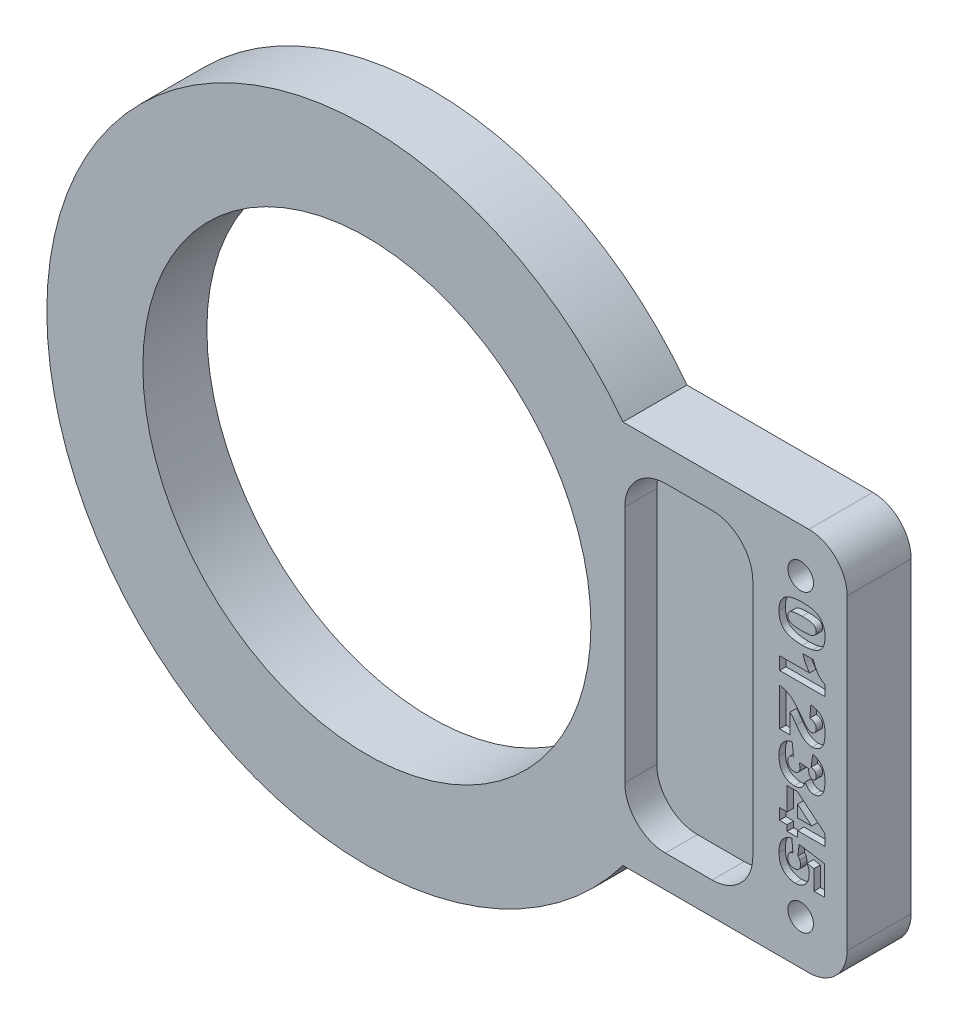
SolidWorks part; units mm, degrees
ref_plane "Front Plane" through (0, 0, 0) normal (0, 0, 1) x (1, 0, 0)
ref_plane "Top Plane" through (0, 0, 0) normal (0, 1, 0) x (1, 0, 0)
ref_plane "Right Plane" through (0, 0, 0) normal (1, 0, 0) x (0, 0, -1)
sketch "Model" plane through (0, 0, 0) normal (0, 0, 1) x (1, 0, 0)
  line L0 (100.7964, -32.5754) -> (97.3961, -32.5754)
  line L1 (97.3961, -32.5754) -> (97.3961, -31.6358)
  line L2 (97.3961, -31.6358) -> (99.6242, -31.6358)
  line L3 (99.1385, -30.6596) -> (99.9, -30.6596)
  line L4 (100.7964, -31.8068) -> (100.7964, -32.5754)
  line L5 (97.3961, -36.3039) -> (97.3961, -33.5172)
  line L6 (99.6538, -34.5161) -> (99.7287, -33.5857)
  line L7 (98.1534, -34.8535) -> (98.1534, -36.3039)
  line L8 (98.1534, -36.3039) -> (97.3961, -36.3039)
  line L9 (99.772, -37.6015) -> (99.9295, -36.7234)
  line L10 (98.2788, -36.6732) -> (98.4016, -37.6015)
  line L11 (98.8394, -37.7541) -> (99.5029, -37.802)
  line L12 (98.7415, -41.4121) -> (99.7934, -41.4121)
  line L13 (99.7934, -41.4121) -> (98.7415, -40.518)
  line L14 (98.7415, -40.518) -> (98.7415, -41.4121)
  line L15 (98.0209, -41.4121) -> (98.0209, -39.7201)
  line L16 (98.0209, -39.7201) -> (98.7848, -39.7201)
  line L17 (98.7848, -39.7201) -> (100.7964, -41.4121)
  line L18 (100.7964, -41.4121) -> (100.7964, -42.2217)
  line L19 (100.7964, -42.2217) -> (98.7415, -42.2217)
  line L20 (98.7415, -42.2217) -> (98.7415, -42.6414)
  line L21 (98.7415, -42.6414) -> (98.0209, -42.6414)
  line L22 (98.0209, -42.6414) -> (98.0209, -42.2217)
  line L23 (98.0209, -42.2217) -> (97.3961, -42.2217)
  line L24 (97.3961, -42.2217) -> (97.3961, -41.4121)
  line L25 (97.3961, -41.4121) -> (98.0209, -41.4121)
  line L26 (100.7393, -43.307) -> (100.7393, -45.5122)
  line L27 (100.7393, -45.5122) -> (99.9978, -45.5122)
  line L28 (99.9978, -45.5122) -> (99.9978, -44.0185)
  line L29 (99.9978, -44.0185) -> (99.4963, -43.9387)
  line L30 (98.2625, -42.8921) -> (98.3654, -43.8317)
  line L31 (98.8282, -43.8042) -> (98.9423, -43.0129)
  line L32 (98.9423, -43.0129) -> (100.7393, -43.307)
  line L33 (99.6589, -21.5138) -> (85.3342, -21.5138)
  line L34 (85.3342, -51.5138) -> (99.6589, -51.5138)
  line L35 (102.8339, -48.3388) -> (102.8339, -24.6888)
  line L36 (92.3025, -49.0138) -> (88.6525, -49.0138)
  line L37 (85.4775, -45.8388) -> (85.4775, -27.1888)
  line L38 (88.6525, -24.0138) -> (92.3025, -24.0138)
  line L39 (95.4775, -27.1888) -> (95.4775, -45.8388)
  circle A0 centre (99.2184, -24.9849) radius 1
  circle A1 centre (99.2184, -48.0427) radius 1
  circle A2 centre (65.3339, -36.5138) radius 17.5
  spline S0 degree 3 poles (99.9443, -28.3794) (99.7883, -28.3109) (99.4999, -28.2767) (99.0789, -28.2767) knots 8 8 8 8 9 9 9 9
  spline S1 degree 3 poles (99.9489, -29.0509) (100.1018, -28.9757) (100.1782, -28.8628) (100.1782, -28.7122) (100.1782, -28.5588) (100.1002, -28.4477) (99.9443, -28.3794) knots 6 6 6 6 7 7 7 8 8 8 8
  spline S2 degree 3 poles (98.0724, -28.962) (98.1381, -29.0313) (98.2431, -29.0822) (98.5285, -29.1475) (98.7512, -29.1638) (99.0539, -29.1638) (99.4978, -29.1638) (99.796, -29.1263) (99.9489, -29.0509) knots 3 3 3 3 4 4 5 5 5 6 6 6 6
  spline S3 degree 3 poles (98.2069, -28.3896) (98.051, -28.4648) (97.973, -28.5739) (97.973, -28.7168) (97.973, -28.8111) (98.0061, -28.8929) (98.0724, -28.962) knots 1 1 1 1 2 2 2 3 3 3 3
  spline S4 degree 3 poles (99.0789, -28.2767) (98.6534, -28.2767) (98.3623, -28.3144) (98.2069, -28.3896) knots 0 0 0 0 1 1 1 1
  spline S5 degree 3 poles (97.868, -27.6109) (97.9913, -27.5304) (98.1595, -27.4677) (98.5866, -27.378) (98.8231, -27.3555) (99.0815, -27.3555) knots 11 11 11 11 12 12 13 13 13 13
  spline S6 degree 3 poles (97.4735, -28.0375) (97.5632, -27.8639) (97.6947, -27.7217) (97.868, -27.6109) knots 10 10 10 10 11 11 11 11
  spline S7 degree 3 poles (97.761, -29.7797) (97.4796, -29.5743) (97.339, -29.2209) (97.339, -28.7191) (97.339, -28.4378) (97.3838, -28.2107) (97.4735, -28.0375) knots 8 8 8 8 9 9 9 10 10 10 10
  spline S8 degree 3 poles (99.8724, -29.994) (99.6232, -30.0562) (99.3633, -30.0875) (99.0927, -30.0875) (98.4862, -30.0875) (98.0423, -29.9848) (97.761, -29.7797) knots 6 6 6 6 7 7 7 8 8 8 8
  spline S9 degree 3 poles (100.2159, -29.8673) (100.1176, -29.9198) (100.0034, -29.9621) (99.8724, -29.994) knots 5 5 5 5 6 6 6 6
  spline S10 degree 3 poles (100.4962, -29.6518) (100.4076, -29.743) (100.3138, -29.8148) (100.2159, -29.8673) knots 4 4 4 4 5 5 5 5
  spline S11 degree 3 poles (100.4152, -27.6988) (100.669, -27.9274) (100.7964, -28.276) (100.7964, -28.7443) (100.7964, -28.9693) (100.7684, -29.1538) (100.6573, -29.4428) (100.5854, -29.5605) (100.4962, -29.6518) knots 1 1 1 1 2 2 2 3 3 4 4 4 4
  spline S12 degree 3 poles (99.0815, -27.3555) (99.717, -27.3555) (100.1614, -27.47) (100.4152, -27.6988) knots 0 0 0 0 1 1 1 1
  spline S13 degree 3 poles (99.6242, -31.6358) (99.5085, -31.4837) (99.4148, -31.3367) (99.3434, -31.1945) knots 3 3 3 3 4 4 4 4
  spline S14 degree 3 poles (99.3434, -31.1945) (99.2721, -31.0523) (99.2038, -30.8742) (99.1385, -30.6596) knots 4 4 4 4 5 5 5 5
  spline S15 degree 3 poles (99.9, -30.6596) (100.0019, -30.9758) (100.1242, -31.2215) (100.2669, -31.3963) knots 6 6 6 6 7 7 7 7
  spline S16 degree 3 poles (100.2669, -31.3963) (100.4101, -31.5711) (100.5865, -31.7079) (100.7964, -31.8068) knots 7 7 7 7 8 8 8 8
  spline S17 degree 3 poles (97.3961, -33.5172) (97.6713, -33.5493) (97.9302, -33.6461) (98.1728, -33.8079) knots 1 1 1 1 2 2 2 2
  spline S18 degree 3 poles (98.1728, -33.8079) (98.4148, -33.97) (98.7013, -34.2735) (99.031, -34.7189) knots 2 2 2 2 3 3 3 3
  spline S19 degree 3 poles (99.031, -34.7189) (99.2333, -34.9911) (99.3867, -35.1651) (99.4917, -35.2413) knots 3 3 3 3 4 4 4 4
  spline S20 degree 3 poles (99.4917, -35.2413) (99.5967, -35.3173) (99.6961, -35.3552) (99.7904, -35.3552) knots 4 4 4 4 5 5 5 5
  spline S21 degree 3 poles (99.7904, -35.3552) (99.8923, -35.3552) (99.9795, -35.3178) (100.0518, -35.2423) knots 5 5 5 5 6 6 6 6
  spline S22 degree 3 poles (100.0518, -35.2423) (100.1237, -35.1672) (100.1599, -35.0726) (100.1599, -34.9585) knots 6 6 6 6 7 7 7 7
  spline S23 degree 3 poles (100.1599, -34.9585) (100.1599, -34.84) (100.1227, -34.7429) (100.0483, -34.6677) knots 7 7 7 7 8 8 8 8
  spline S24 degree 3 poles (100.0483, -34.6677) (99.9739, -34.5925) (99.8424, -34.5418) (99.6538, -34.5161) knots 8 8 8 8 9 9 9 9
  spline S25 degree 3 poles (99.7287, -33.5857) (99.9902, -33.6222) (100.1945, -33.6889) (100.3413, -33.7863) knots 10 10 10 10 11 11 11 11
  spline S26 degree 3 poles (100.3413, -33.7863) (100.4881, -33.8836) (100.6002, -34.0207) (100.6787, -34.1981) knots 11 11 11 11 12 12 12 12
  spline S27 degree 3 poles (100.6787, -34.1981) (100.7572, -34.3752) (100.7964, -34.6203) (100.7964, -34.9335) knots 12 12 12 12 13 13 13 13
  spline S28 degree 3 poles (100.7964, -34.9335) (100.7964, -35.2602) (100.7587, -35.5145) (100.6843, -35.6962) knots 13 13 13 13 14 14 14 14
  spline S29 degree 3 poles (100.6843, -35.6962) (100.6099, -35.8779) (100.4957, -36.0208) (100.3413, -36.125) knots 14 14 14 14 15 15 15 15
  spline S30 degree 3 poles (100.3413, -36.125) (100.1869, -36.229) (100.0141, -36.2813) (99.8225, -36.2813) knots 15 15 15 15 16 16 16 16
  spline S31 degree 3 poles (99.8225, -36.2813) (99.6186, -36.2813) (99.4239, -36.2214) (99.2384, -36.1021) knots 16 16 16 16 17 17 17 17
  spline S32 degree 3 poles (99.2384, -36.1021) (99.0529, -35.9829) (98.8496, -35.7657) (98.6274, -35.451) knots 17 17 17 17 18 18 18 18
  spline S33 degree 3 poles (98.6274, -35.451) (98.4984, -35.264) (98.4077, -35.1389) (98.3562, -35.0759) knots 18 18 18 18 19 19 19 19
  spline S34 degree 3 poles (98.3562, -35.0759) (98.3042, -35.0127) (98.237, -34.9386) (98.1534, -34.8535) knots 19 19 19 19 20 20 20 20
  spline S35 degree 3 poles (99.9295, -36.7234) (100.2093, -36.7965) (100.4239, -36.9367) (100.5727, -37.1441) knots 1 1 1 1 2 2 2 2
  spline S36 degree 3 poles (100.5727, -37.1441) (100.7215, -37.3518) (100.7964, -37.6456) (100.7964, -38.0255) knots 2 2 2 2 3 3 3 3
  spline S37 degree 3 poles (100.7964, -38.0255) (100.7964, -38.4618) (100.7149, -38.7773) (100.5523, -38.9719) knots 3 3 3 3 4 4 4 4
  spline S38 degree 3 poles (100.5523, -38.9719) (100.3897, -39.1666) (100.1848, -39.264) (99.9387, -39.264) knots 4 4 4 4 5 5 5 5
  spline S39 degree 3 poles (99.9387, -39.264) (99.7945, -39.264) (99.6635, -39.2242) (99.5463, -39.1452) knots 5 5 5 5 6 6 6 6
  spline S40 degree 3 poles (99.5463, -39.1452) (99.4296, -39.0662) (99.3266, -38.947) (99.2384, -38.7872) knots 6 6 6 6 7 7 7 7
  spline S41 degree 3 poles (99.2384, -38.7872) (99.2068, -38.9164) (99.1696, -39.0153) (99.1268, -39.0838) knots 7 7 7 7 8 8 8 8
  spline S42 degree 3 poles (99.1268, -39.0838) (99.0585, -39.1947) (98.9683, -39.281) (98.8567, -39.3424) knots 8 8 8 8 9 9 9 9
  spline S43 degree 3 poles (98.8567, -39.3424) (98.7451, -39.4041) (98.6116, -39.435) (98.4566, -39.435) knots 9 9 9 9 10 10 10 10
  spline S44 degree 3 poles (98.4566, -39.435) (98.2619, -39.435) (98.0754, -39.384) (97.8965, -39.2821) knots 10 10 10 10 11 11 11 11
  spline S45 degree 3 poles (97.8965, -39.2821) (97.7182, -39.1801) (97.5806, -39.0336) (97.4837, -38.842) knots 11 11 11 11 12 12 12 12
  spline S46 degree 3 poles (97.4837, -38.842) (97.3874, -38.6503) (97.339, -38.3988) (97.339, -38.0872) knots 12 12 12 12 13 13 13 13
  spline S47 degree 3 poles (97.339, -38.0872) (97.339, -37.7829) (97.3747, -37.5431) (97.446, -37.3676) knots 13 13 13 13 14 14 14 14
  spline S48 degree 3 poles (97.446, -37.3676) (97.5179, -37.192) (97.6223, -37.0475) (97.7599, -36.9344) knots 14 14 14 14 15 15 15 15
  spline S49 degree 3 poles (97.7599, -36.9344) (97.8976, -36.821) (98.0703, -36.7341) (98.2788, -36.6732) knots 15 15 15 15 16 16 16 16
  spline S50 degree 3 poles (98.4016, -37.6015) (98.2146, -37.6379) (98.0851, -37.6945) (98.0127, -37.7712) knots 17 17 17 17 18 18 18 18
  spline S51 degree 3 poles (98.0127, -37.7712) (97.9409, -37.8482) (97.9047, -37.9458) (97.9047, -38.0643) knots 18 18 18 18 19 19 19 19
  spline S52 degree 3 poles (97.9047, -38.0643) (97.9047, -38.1889) (97.95, -38.2928) (98.0413, -38.3756) knots 19 19 19 19 20 20 20 20
  spline S53 degree 3 poles (98.0413, -38.3756) (98.1325, -38.4585) (98.2543, -38.5) (98.4062, -38.5) knots 20 20 20 20 21 21 21 21
  spline S54 degree 3 poles (98.4062, -38.5) (98.5611, -38.5) (98.6814, -38.46) (98.7665, -38.3802) knots 21 21 21 21 22 22 22 22
  spline S55 degree 3 poles (98.7665, -38.3802) (98.8516, -38.3005) (98.8944, -38.1919) (98.8944, -38.0551) knots 22 22 22 22 23 23 23 23
  spline S56 degree 3 poles (98.8944, -38.0551) (98.8944, -37.9822) (98.8761, -37.8818) (98.8394, -37.7541) knots 23 23 23 23 24 24 24 24
  spline S57 degree 3 poles (99.5029, -37.802) (99.4958, -37.8538) (99.4917, -37.894) (99.4917, -37.9228) knots 25 25 25 25 26 26 26 26
  spline S58 degree 3 poles (99.4917, -37.9228) (99.4917, -38.0446) (99.5305, -38.1461) (99.6079, -38.2273) knots 26 26 26 26 27 27 27 27
  spline S59 degree 3 poles (99.6079, -38.2273) (99.6854, -38.3086) (99.7776, -38.3494) (99.8842, -38.3494) knots 27 27 27 27 28 28 28 28
  spline S60 degree 3 poles (99.8842, -38.3494) (99.9861, -38.3494) (100.0671, -38.3191) (100.1283, -38.2582) knots 28 28 28 28 29 29 29 29
  spline S61 degree 3 poles (100.1283, -38.2582) (100.1889, -38.1973) (100.219, -38.1137) (100.219, -38.0074) knots 29 29 29 29 30 30 30 30
  spline S62 degree 3 poles (100.219, -38.0074) (100.219, -37.8979) (100.1864, -37.8089) (100.1201, -37.7406) knots 30 30 30 30 31 31 31 31
  spline S63 degree 3 poles (100.1201, -37.7406) (100.0539, -37.6721) (99.9382, -37.6257) (99.772, -37.6015) knots 31 31 31 31 32 32 32 32
  spline S64 degree 3 poles (99.4963, -43.9387) (99.5447, -44.0422) (99.5814, -44.1443) (99.6059, -44.2455) knots 4 4 4 4 5 5 5 5
  spline S65 degree 3 poles (99.6059, -44.2455) (99.6304, -44.3467) (99.6421, -44.4466) (99.6421, -44.5454) knots 5 5 5 5 6 6 6 6
  spline S66 degree 3 poles (99.6421, -44.5454) (99.6421, -44.8798) (99.5412, -45.1512) (99.3388, -45.3596) knots 6 6 6 6 7 7 7 7
  spline S67 degree 3 poles (99.3388, -45.3596) (99.137, -45.5678) (98.8822, -45.672) (98.5749, -45.672) knots 7 7 7 7 8 8 8 8
  spline S68 degree 3 poles (98.5749, -45.672) (98.3593, -45.672) (98.1519, -45.6182) (97.9526, -45.5112) knots 8 8 8 8 9 9 9 9
  spline S69 degree 3 poles (97.9526, -45.5112) (97.7533, -45.4039) (97.6014, -45.2518) (97.4965, -45.0551) knots 9 9 9 9 10 10 10 10
  spline S70 degree 3 poles (97.4965, -45.0551) (97.3915, -44.8581) (97.339, -44.6061) (97.339, -44.299) knots 10 10 10 10 11 11 11 11
  spline S71 degree 3 poles (97.339, -44.299) (97.339, -44.0786) (97.3599, -43.8898) (97.4017, -43.7323) knots 11 11 11 11 12 12 12 12
  spline S72 degree 3 poles (97.4017, -43.7323) (97.4435, -43.5751) (97.5056, -43.4413) (97.5887, -43.3309) knots 12 12 12 12 13 13 13 13
  spline S73 degree 3 poles (97.5887, -43.3309) (97.6718, -43.2209) (97.7656, -43.1314) (97.8705, -43.0631) knots 13 13 13 13 14 14 14 14
  spline S74 degree 3 poles (97.8705, -43.0631) (97.9755, -42.9946) (98.106, -42.9378) (98.2625, -42.8921) knots 14 14 14 14 15 15 15 15
  spline S75 degree 3 poles (98.3654, -43.8317) (98.2146, -43.8544) (98.1004, -43.9076) (98.0219, -43.9912) knots 16 16 16 16 17 17 17 17
  spline S76 degree 3 poles (98.0219, -43.9912) (97.9439, -44.0748) (97.9047, -44.1744) (97.9047, -44.2899) knots 17 17 17 17 18 18 18 18
  spline S77 degree 3 poles (97.9047, -44.2899) (97.9047, -44.419) (97.9536, -44.5261) (98.0515, -44.6104) knots 18 18 18 18 19 19 19 19
  spline S78 degree 3 poles (98.0515, -44.6104) (98.1498, -44.6948) (98.2961, -44.7368) (98.4908, -44.7368) knots 19 19 19 19 20 20 20 20
  spline S79 degree 3 poles (98.4908, -44.7368) (98.6901, -44.7368) (98.8358, -44.6943) (98.9286, -44.6091) knots 20 20 20 20 21 21 21 21
  spline S80 degree 3 poles (98.9286, -44.6091) (99.0213, -44.524) (99.0677, -44.4109) (99.0677, -44.2695) knots 21 21 21 21 22 22 22 22
  spline S81 degree 3 poles (99.0677, -44.2695) (99.0677, -44.1798) (99.0458, -44.0931) (99.0014, -44.0095) knots 22 22 22 22 23 23 23 23
  spline S82 degree 3 poles (99.0014, -44.0095) (98.9693, -43.9471) (98.9117, -43.8786) (98.8282, -43.8042) knots 23 23 23 23 24 24 24 24
  spline S83 degree 3 poles (85.3342, -21.5138) (80.7731, -15.442) (73.5126, -11.5138) (65.3339, -11.5138) knots 1 1 1 1 2 2 2 2
  spline S84 degree 3 poles (65.3339, -11.5138) (51.5268, -11.5138) (40.3339, -22.7067) (40.3339, -36.5138) knots 2 2 2 2 3 3 3 3
  spline S85 degree 3 poles (40.3339, -36.5138) (40.3339, -50.3209) (51.5268, -61.5138) (65.3339, -61.5138) knots 3 3 3 3 4 4 4 4
  spline S86 degree 3 poles (65.3339, -61.5138) (73.5126, -61.5138) (80.7731, -57.5856) (85.3342, -51.5138) knots 4 4 4 4 5 5 5 5
  spline S87 degree 3 poles (99.6589, -51.5138) (101.4052, -51.5138) (102.8339, -50.085) (102.8339, -48.3388) knots 6 6 6 6 7 7 7 7
  spline S88 degree 3 poles (102.8339, -24.6888) (102.8339, -22.9425) (101.4052, -21.5138) (99.6589, -21.5138) knots 8 8 8 8 9 9 9 9
  spline S89 degree 3 poles (88.6525, -49.0138) (86.9063, -49.0138) (85.4775, -47.585) (85.4775, -45.8388) knots 1 1 1 1 2 2 2 2
  spline S90 degree 3 poles (85.4775, -27.1888) (85.4775, -25.4425) (86.9063, -24.0138) (88.6525, -24.0138) knots 3 3 3 3 4 4 4 4
  spline S91 degree 3 poles (92.3025, -24.0138) (94.0488, -24.0138) (95.4775, -25.4425) (95.4775, -27.1888) knots 5 5 5 5 6 6 6 6
  spline S92 degree 3 poles (95.4775, -45.8388) (95.4775, -47.585) (94.0488, -49.0138) (92.3025, -49.0138) knots 7 7 7 7 8 8 8 8
sketch "Sketch3" plane through (0, 0, 0) normal (0, 0, 1) x (1, 0, 0)
  line L1 (77.8189, -51.5138) -> (99.8494, -51.5138)
  line L2 (77.8189, -51.5138) -> (77.8189, -21.5138)
  line L3 (77.8189, -21.5138) -> (99.8494, -21.5138)
  line L4 (102.8494, -48.5138) -> (102.8494, -24.5138)
  line L5 (77.8189, -51.5138) -> (102.8494, -21.5138) construction
  line L6 (77.8189, -21.5138) -> (102.8494, -51.5138) construction
  line L7 (88.101, -49.0148) -> (92.5672, -49.0148)
  line L8 (85.101, -46.0148) -> (85.101, -27.0127)
  line L9 (88.101, -24.0127) -> (92.5672, -24.0127)
  line L10 (95.5672, -46.0148) -> (95.5672, -27.0127)
  line L11 (85.101, -49.0148) -> (95.5672, -24.0127) construction
  line L12 (85.101, -24.0127) -> (95.5672, -49.0148) construction
  circle A0 centre (65.3339, -36.5138) radius 17.5
  circle A1 centre (65.3339, -36.5138) radius 25.0002
  arc A2 (99.8494, -51.5138) -> (102.8494, -48.5138) centre (99.8494, -48.5138) ccw
  arc A3 (99.8494, -21.5138) -> (102.8494, -24.5138) centre (99.8494, -24.5138) cw
  circle A4 centre (99.2184, -24.9849) radius 1
  circle A5 centre (99.2184, -48.0427) radius 1
  arc A6 (88.101, -49.0148) -> (85.101, -46.0148) centre (88.101, -46.0148) cw
  arc A7 (92.5672, -49.0148) -> (95.5672, -46.0148) centre (92.5672, -46.0148) ccw
  arc A8 (92.5672, -24.0127) -> (95.5672, -27.0127) centre (92.5672, -27.0127) cw
  arc A9 (85.101, -27.0127) -> (88.101, -24.0127) centre (88.101, -27.0127) cw
  point P5 (90.3341, -36.5138)
  point P22 (90.3341, -36.5138)
  dimension "D1" = 35
  dimension "D2" = 3
  dimension "D3" = 3
extrude "Boss-Extrude1" add sketch "Sketch3" against normal blind 5 contours L3 A1 L1 L2 A0 | L8 A9 A1 L3 L2 A0 L1 A6 | A1 A9 L9 A8 L10 A7 L7 A6 L1 A2 L4 A3 L3 A5 A4 | A9 A1 A6 L7 A7 L10 A8 L9 | A9 L8 A6 A1
sketch "Sketch4" plane through (0, 0, 0) normal (0, 0, 1) x (1, 0, 0)
  line L3 (99.8494, -21.5138) -> (85.3342, -21.5138)
  line L4 (85.3342, -51.5138) -> (99.8494, -51.5138)
  line L5 (102.8494, -48.5138) -> (102.8494, -24.5138)
  line L6 (99.8494, -21.5138) -> (85.3342, -21.5138)
  line L7 (85.3342, -51.5138) -> (99.8494, -51.5138)
  line L8 (102.8494, -48.5138) -> (102.8494, -24.5138)
  arc A3 (85.3342, -21.5138) -> (85.3342, -51.5138) centre (65.3339, -36.5138) ccw
  arc A4 (99.8494, -51.5138) -> (102.8494, -48.5138) centre (99.8494, -48.5138) ccw
  arc A5 (102.8494, -24.5138) -> (99.8494, -21.5138) centre (99.8494, -24.5138) ccw
  arc A6 (85.3342, -21.5138) -> (85.3342, -51.5138) centre (65.3339, -36.5138) ccw
  arc A7 (99.8494, -51.5138) -> (102.8494, -48.5138) centre (99.8494, -48.5138) ccw
  arc A8 (102.8494, -24.5138) -> (99.8494, -21.5138) centre (99.8494, -24.5138) ccw
  dimension "D1" = 0
extrude "Cut-Extrude1" cut sketch "Model" against normal blind 2.5 contours L39 S92 L36 S89 L37 S90 L38 S91
sketch "Sketch5" plane through (134.1721, 79.4655, 0) normal (0, 0, 1) x (0, -1, 0)
  text T0 "012345" font "Arial Black" height 3.5
extrude "Cut-Extrude2" cut sketch "Sketch5" against normal blind 0.5
